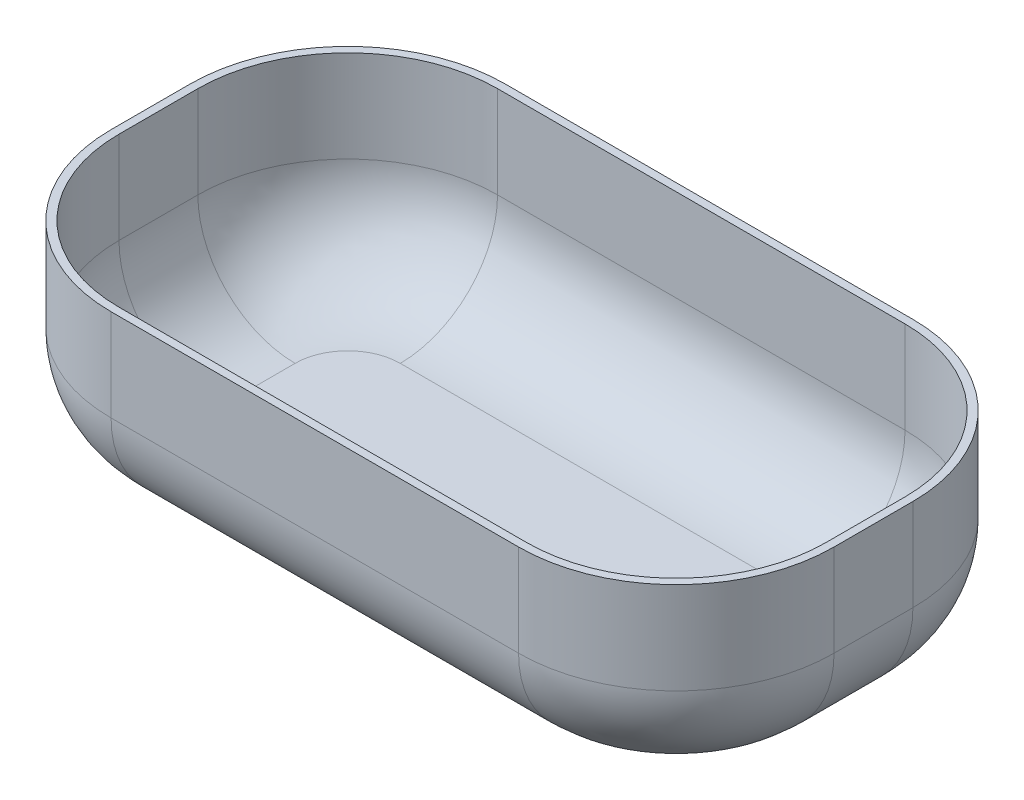
SolidWorks part; units mm, degrees
material "PET"
ref_plane "Alzado" through (0, 0, 0) normal (0, 0, 1) x (1, 0, 0)
ref_plane "Planta" through (0, 0, 0) normal (0, 1, 0) x (1, 0, 0)
ref_plane "Vista lateral" through (0, 0, 0) normal (1, 0, 0) x (0, 0, -1)
sketch "Croquis1" plane through (0, 0, 0) normal (0, 0, 1) x (1, 0, 0)
  line L0 (-7718.8128, 0) -> (378221.8282, 0) construction
  line L2 (275, 0) -> (275, -150)
  line L3 (275, -150) -> (-275, -150)
  line L4 (-275, 0) -> (-275, -150)
  line L7 (-275, 0) -> (275, 0)
  point P0 (0, 0)
  point P2 (0, 0)
  dimension "D1" = 550
  dimension "D2" = 150
extrude "Saliente-Extruir1" add sketch "Croquis1" along normal mid plane 300
fillet "Redondeo1" radius 120 4 edges at (275, -75, -150) (275, -75, 150) (-275, -75, -150) (-275, -75, 150)
fillet "Redondeo2" radius 80 8 edges at (-239.8528, -150, -114.8528) (-275, -150, 0) (-239.8528, -150, 114.8528) (0, -150, 150) (239.8528, -150, 114.8528) (275, -150, 0) (239.8528, -150, -114.8528) (0, -150, -150)
shell "Vaciado1" thickness 6
